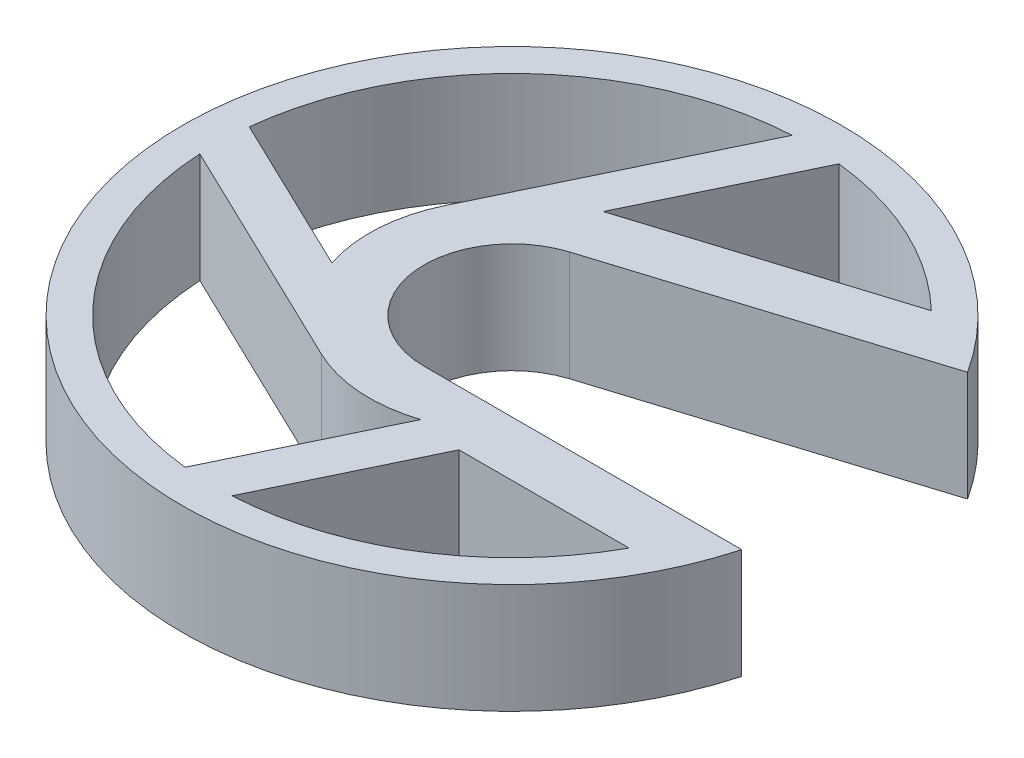
SolidWorks part; units mm, degrees
ref_plane "前视基准面" through (0, 0, 0) normal (0, 0, 1) x (1, 0, 0)
ref_plane "上视基准面" through (0, 0, 0) normal (0, 1, 0) x (1, 0, 0)
ref_plane "右视基准面" through (0, 0, 0) normal (1, 0, 0) x (0, 0, -1)
sketch "草图1" plane through (0, 0, 0) normal (0, 1, 0) x (1, 0, 0)
  line L0 (-59.407, 0) -> (47.93, 0) construction
  line L1 (0, 0) -> (0, 18.582) construction
  line L2 (-59.407, 0) -> (0, 18.582) construction
  line L3 (0, 18.582) -> (47.93, 0) construction
  line L4 (-59.407, 0) -> (0, 18.582) construction
  line L5 (-60.6011, 3.8176) -> (-1.1941, 22.3996) construction
  line L6 (-58.2129, -3.8176) -> (1.1941, 14.7644) construction
  line L7 (0, 18.582) -> (47.93, 0) construction
  line L8 (1.4459, 22.3115) -> (49.3759, 3.7295) construction
  line L9 (-1.4459, 14.8525) -> (46.4841, -3.7295) construction
  line L10 (-59.407, 0) -> (47.93, 0) construction
  line L11 (-59.407, 4) -> (47.93, 4) construction
  line L12 (-59.407, -4) -> (47.93, -4) construction
  line L13 (-59.407, -4) -> (-44.9502, -4)
  line L14 (-60.6011, 3.8176) -> (-46.8035, 8.1334)
  line L15 (-59.407, -6.5) -> (-45.8885, -6.5)
  line L16 (-61.3474, 6.2036) -> (-48.4454, 10.2393)
  line L17 (-62.2237, -5.858) -> (-74.407, 0)
  line L18 (-74.2528, 2.1451) -> (-65.5842, -2.023)
  line L19 (-65.265, 2.8167) -> (-59.407, 15)
  line L20 (-57.2619, 14.8458) -> (-61.43, 6.1772)
  line L21 (-53.549, -2.8167) -> (-59.407, -15)
  line L22 (-61.5521, -14.8458) -> (-57.384, -6.1772)
  arc A0 (-60.6011, 3.8176) -> (-58.2129, -3.8176) centre (-59.407, 0) ccw construction
  arc A1 (1.1941, 14.7644) -> (-1.1941, 22.3996) centre (0, 18.582) ccw construction
  arc A2 (1.4459, 22.3115) -> (-1.4459, 14.8525) centre (0, 18.582) ccw construction
  arc A3 (46.4841, -3.7295) -> (49.3759, 3.7295) centre (47.93, 0) ccw construction
  arc A4 (-59.407, 4) -> (-59.407, -4) centre (-59.407, 0) ccw construction
  arc A5 (47.93, -4) -> (47.93, 4) centre (47.93, 0) ccw construction
  circle A7 centre (0, 18.582) radius 1.95 construction
  circle A8 centre (47.93, 0) radius 1.95 construction
  circle A9 centre (-59.407, 0) radius 15
  circle A10 centre (-59.407, 0) radius 4
  circle A11 centre (-59.407, 0) radius 6.5
  circle A12 centre (-59.407, 0) radius 13.5
  point P3 (-5.7385, 0)
  point P5 (-29.7035, 9.291)
  point P10 (23.965, 9.291)
  point P16 (-5.7385, 0)
  dimension "D4" = 4
  dimension "D5" = 4
  dimension "D7" = 30
  dimension "D8" = 13
  dimension "D12" = 27
  dimension "D1" = 18.582
  dimension "D2" = 107.337
  dimension "D3" = 47.93
  dimension "D6" = 8
  dimension "D9" = 2
  dimension "D10" = 2
  dimension "D11" = 2
extrude "凸台-拉伸1" add sketch "草图1" along normal blind 5 contours A12 L16 A9 L20 | A12 L14 A9 L16 | A12 L19 A9 L18 | A12 L20 A9 L19 | A12 L18 A9 L17 | A12 L17 A9 L22 | A12 L22 A9 L21 | A12 L21 A9 L15 | A12 L15 A9 L13 | L18 A12 L17 A11 | L22 A12 L21 L15 | L14 A12 L16 A11 | A11 L13 A10 L14 | A11 L22 L15 L21 L13 | L15 A12 L13 L21 | L20 A12 L19 A11
